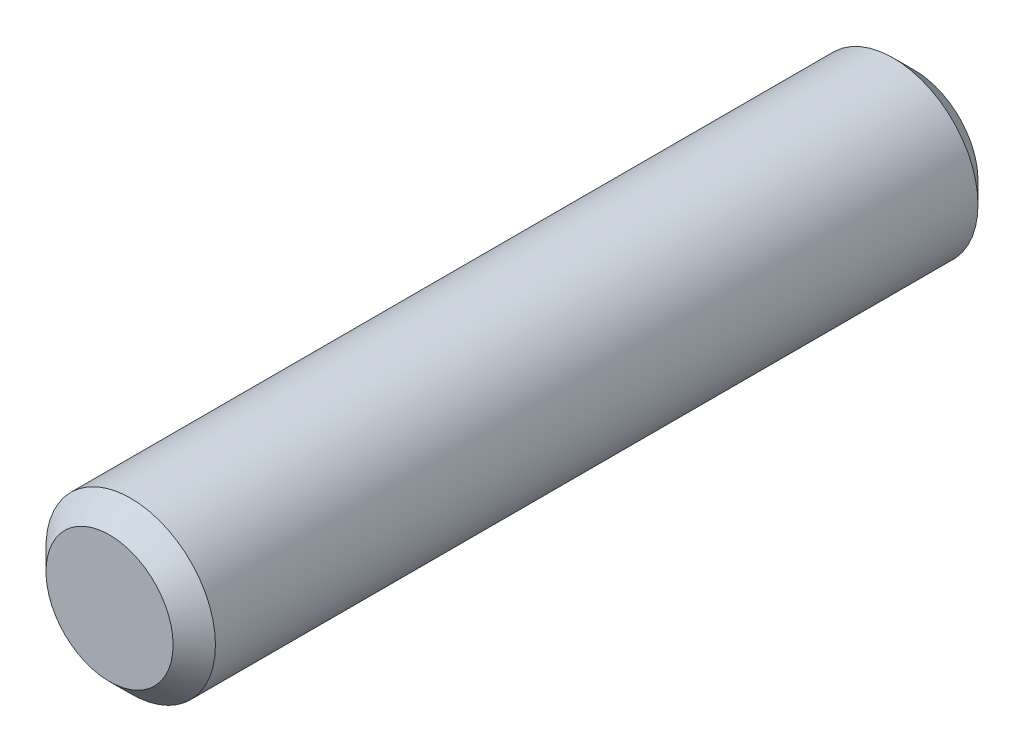
SolidWorks part; units mm, degrees
ref_plane "Front Plane" through (0, 0, 0) normal (0, 0, 1) x (1, 0, 0)
ref_plane "Top Plane" through (0, 0, 0) normal (0, 1, 0) x (1, 0, 0)
ref_plane "Right Plane" through (0, 0, 0) normal (1, 0, 0) x (0, 0, -1)
sketch "Sketch1" plane through (0, 0, 0) normal (0, 0, 1) x (1, 0, 0)
  circle A0 centre (0, 0) radius 4
  dimension "D1" = 8
extrude "Boss-Extrude1" add sketch "Sketch1" along normal blind 38
chamfer "Chamfer1" distance 1 angle 45 2 edges at (4, 0, 0) (4, 0, 38)
